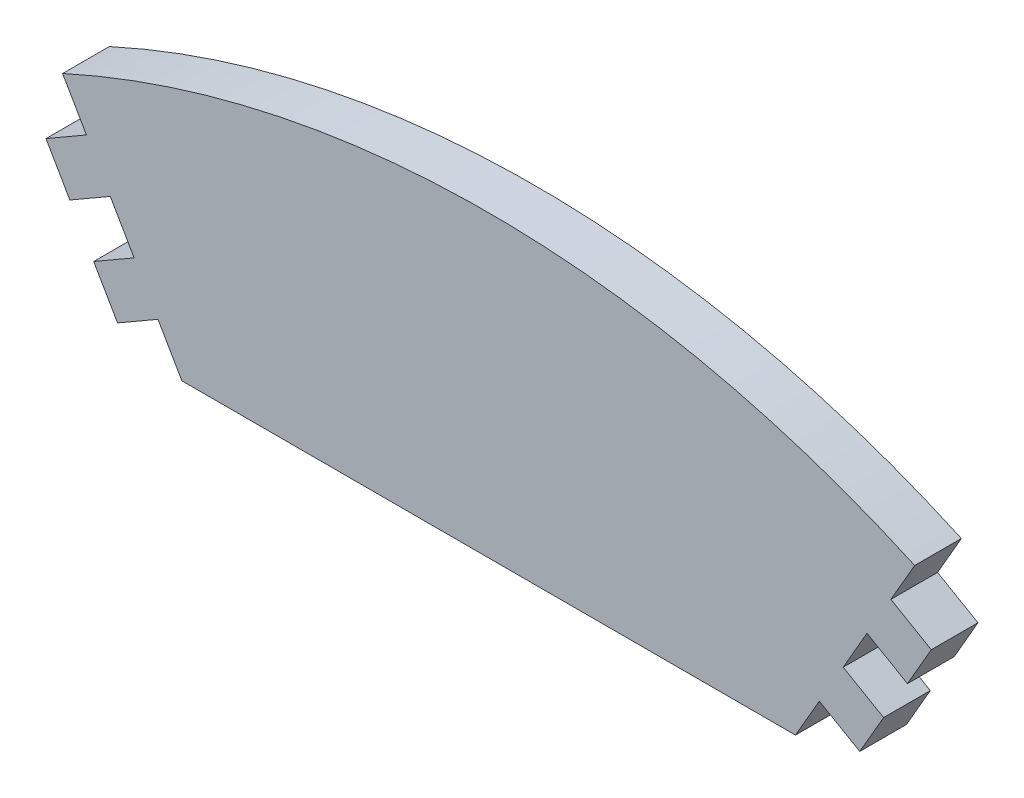
SolidWorks part; units mm, degrees
ref_plane "Front Plane" through (0, 0, 0) normal (0, 0, 1) x (1, 0, 0)
ref_plane "Top Plane" through (0, 0, 0) normal (0, 1, 0) x (1, 0, 0)
ref_plane "Right Plane" through (0, 0, 0) normal (1, 0, 0) x (0, 0, -1)
sketch "Sketch1" plane through (0, 0, 0) normal (0, 0, 1) x (1, 0, 0)
  line L3 (-32.85, 77.9867) -> (32.85, 77.9867)
  line L4 (-32.85, 77.9867) -> (-35.403, 82.4086)
  line L5 (0, 0) -> (0, 126.1957) construction
  line L7 (32.85, 77.9867) -> (35.403, 82.4086)
  line L8 (35.403, 82.4086) -> (39.7331, 79.9086)
  line L9 (39.7331, 79.9086) -> (42.2861, 84.3305)
  line L10 (42.2861, 84.3305) -> (37.956, 86.8305)
  line L11 (37.956, 86.8305) -> (40.509, 91.2525)
  line L12 (40.509, 91.2525) -> (44.8391, 88.7525)
  line L13 (44.8391, 88.7525) -> (47.3921, 93.1744)
  line L14 (47.3921, 93.1744) -> (43.062, 95.6744)
  line L15 (43.062, 95.6744) -> (45.615, 100.0963)
  line L16 (-43.062, 95.6744) -> (-45.615, 100.0963)
  line L17 (-47.3921, 93.1744) -> (-43.062, 95.6744)
  line L18 (-44.8391, 88.7525) -> (-47.3921, 93.1744)
  line L19 (-40.509, 91.2525) -> (-44.8391, 88.7525)
  line L20 (-37.956, 86.8305) -> (-40.509, 91.2525)
  line L21 (-42.2861, 84.3305) -> (-37.956, 86.8305)
  line L22 (-39.7331, 79.9086) -> (-42.2861, 84.3305)
  line L23 (-35.403, 82.4086) -> (-39.7331, 79.9086)
  arc A0 (-45.615, 100.0963) -> (45.615, 100.0963) centre (0, 0) cw
  dimension "D1" = 120
  dimension "D2" = 110
  dimension "D3" = 25.53
  dimension "D4" = 5
  dimension "D5" = 65.7
extrude "Boss-Extrude1" add sketch "Sketch1" along normal blind 5
